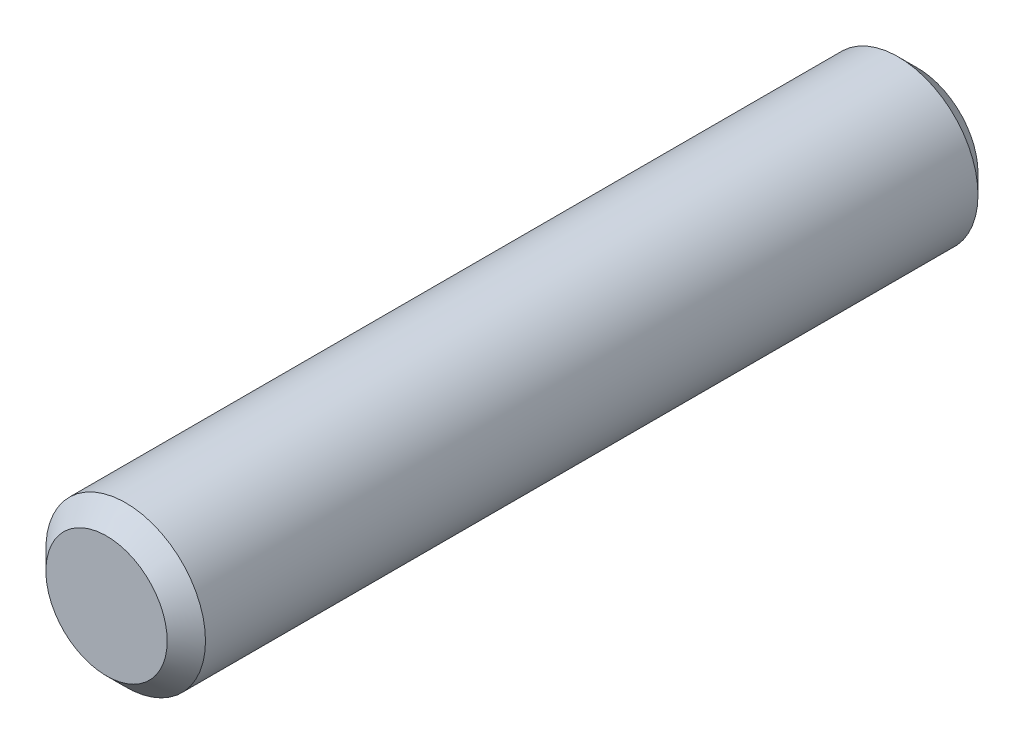
SolidWorks part; units mm, degrees
ref_plane "Front Plane" through (0, 0, 0) normal (0, 0, 1) x (1, 0, 0)
ref_plane "Top Plane" through (0, 0, 0) normal (0, 1, 0) x (1, 0, 0)
ref_plane "Right Plane" through (0, 0, 0) normal (1, 0, 0) x (0, 0, -1)
sketch "Sketch1" plane through (0, 0, 0) normal (0, 0, 1) x (1, 0, 0)
  circle A0 centre (0, 0) radius 12.5
extrude "Boss-Extrude1" add sketch "Sketch1" along normal blind 127
chamfer "Chamfer1" distance 3 angle 45 2 edges at (12.5, 0, 0) (12.5, 0, 127)
